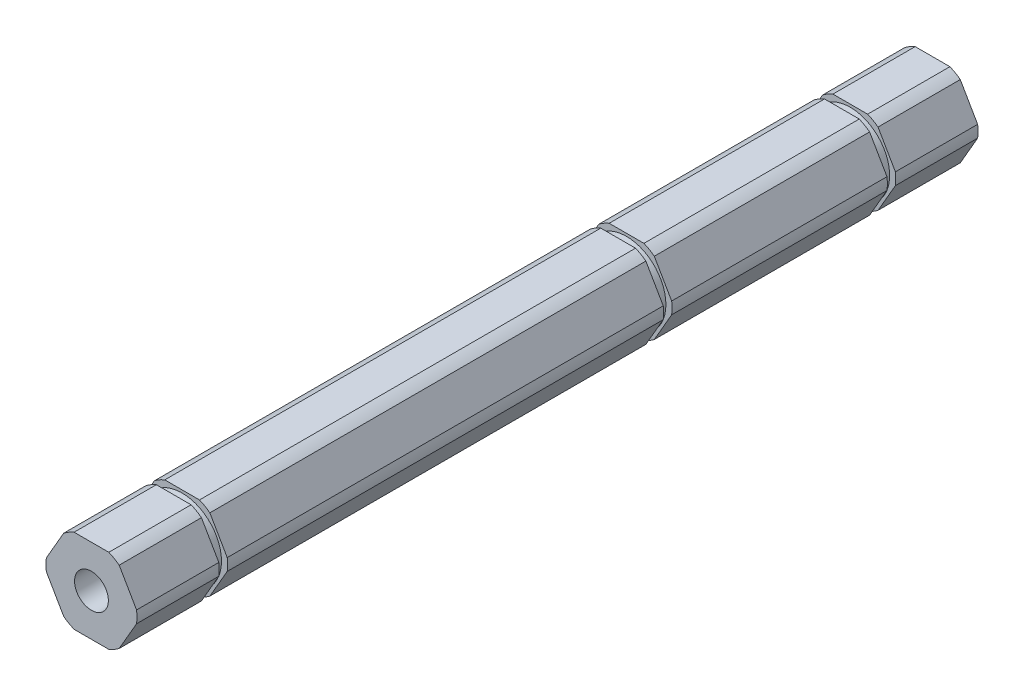
SolidWorks part; units mm, degrees
ref_plane "Front" through (0, 0, 0) normal (0, 0, 1) x (1, 0, 0)
ref_plane "Top" through (0, 0, 0) normal (0, 1, 0) x (1, 0, 0)
ref_plane "Right" through (0, 0, 0) normal (1, 0, 0) x (0, 0, -1)
ref_plane "Plane1" through (0, 0, -17.2974) normal (0, 0, 1) x (1, 0, 0)
sketch "Sketch1" plane through (0, 0, -17.2974) normal (0, 0, 1) x (1, 0, 0)
  line L0 (-4.1874, 5.4472) -> (-6.8111, 0.9028)
  line L1 (-6.8111, -0.9028) -> (-4.1874, -5.4472)
  line L2 (-2.6237, -6.35) -> (2.6237, -6.35)
  line L3 (4.1874, -5.4472) -> (6.8111, -0.9028)
  line L4 (6.8111, 0.9028) -> (4.1874, 5.4472)
  line L5 (2.6237, 6.35) -> (-2.6237, 6.35)
  arc A0 (-2.6237, 6.35) -> (-4.1874, 5.4472) centre (0, 0) ccw
  arc A1 (-6.8111, 0.9028) -> (-6.8111, -0.9028) centre (0, 0) ccw
  arc A2 (-4.1874, -5.4472) -> (-2.6237, -6.35) centre (0, 0) ccw
  arc A3 (2.6237, -6.35) -> (4.1874, -5.4472) centre (0, 0) ccw
  arc A4 (6.8111, -0.9028) -> (6.8111, 0.9028) centre (0, 0) ccw
  arc A5 (4.1874, 5.4472) -> (2.6237, 6.35) centre (0, 0) ccw
extrude "Boss-Extrude1" add sketch "Sketch1" against normal blind 32.512
sketch "Sketch2" plane through (0, 0, -49.8094) normal (0, 0, -1) x (-1, 0, 0)
  circle A0 centre (0, 0) radius 5.9436
extrude "Boss-Extrude2" add sketch "Sketch2" along normal blind 1.27
sketch "Sketch3" plane through (0, 0, -17.2974) normal (0, 0, 1) x (1, 0, 0)
  circle A0 centre (0, 0) radius 5.9436
extrude "Boss-Extrude3" add sketch "Sketch3" along normal blind 1.27
ref_plane "Plane2" through (0, 0, -16.0274) normal (0, 0, -1) x (-1, 0, 0)
sketch "Sketch4" plane through (0, 0, -16.0274) normal (0, 0, -1) x (-1, 0, 0)
  line L0 (2.6237, 6.35) -> (-2.6237, 6.35)
  line L1 (-4.1874, 5.4472) -> (-6.8111, 0.9028)
  line L2 (-6.8111, -0.9028) -> (-4.1874, -5.4472)
  line L3 (-2.6237, -6.35) -> (2.6237, -6.35)
  line L4 (4.1874, -5.4472) -> (6.8111, -0.9028)
  line L5 (6.8111, 0.9028) -> (4.1874, 5.4472)
  arc A0 (4.1874, 5.4472) -> (2.6237, 6.35) centre (0, 0) ccw
  arc A1 (-2.6237, 6.35) -> (-4.1874, 5.4472) centre (0, 0) ccw
  arc A2 (-6.8111, 0.9028) -> (-6.8111, -0.9028) centre (0, 0) ccw
  arc A3 (-4.1874, -5.4472) -> (-2.6237, -6.35) centre (0, 0) ccw
  arc A4 (2.6237, -6.35) -> (4.1874, -5.4472) centre (0, 0) ccw
  arc A5 (6.8111, -0.9028) -> (6.8111, 0.9028) centre (0, 0) ccw
extrude "Boss-Extrude4" add sketch "Sketch4" against normal blind 65.8368
ref_plane "Plane3" through (0, 0, -51.0794) normal (0, 0, 1) x (1, 0, 0)
sketch "Sketch5" plane through (0, 0, -51.0794) normal (0, 0, 1) x (1, 0, 0)
  line L0 (-4.1874, 5.4472) -> (-6.8111, 0.9028)
  line L1 (-6.8111, -0.9028) -> (-4.1874, -5.4472)
  line L2 (-2.6237, -6.35) -> (2.6237, -6.35)
  line L3 (4.1874, -5.4472) -> (6.8111, -0.9028)
  line L4 (6.8111, 0.9028) -> (4.1874, 5.4472)
  line L5 (2.6237, 6.35) -> (-2.6237, 6.35)
  arc A0 (-2.6237, 6.35) -> (-4.1874, 5.4472) centre (0, 0) ccw
  arc A1 (-6.8111, 0.9028) -> (-6.8111, -0.9028) centre (0, 0) ccw
  arc A2 (-4.1874, -5.4472) -> (-2.6237, -6.35) centre (0, 0) ccw
  arc A3 (2.6237, -6.35) -> (4.1874, -5.4472) centre (0, 0) ccw
  arc A4 (6.8111, -0.9028) -> (6.8111, 0.9028) centre (0, 0) ccw
  arc A5 (4.1874, 5.4472) -> (2.6237, 6.35) centre (0, 0) ccw
extrude "Boss-Extrude5" add sketch "Sketch5" against normal blind 12.4206
sketch "Sketch6" plane through (0, 0, 49.8094) normal (0, 0, 1) x (1, 0, 0)
  circle A0 centre (0, 0) radius 5.9436
extrude "Boss-Extrude6" add sketch "Sketch6" along normal blind 1.27
ref_plane "Plane4" through (0, 0, 51.0794) normal (0, 0, -1) x (-1, 0, 0)
sketch "Sketch7" plane through (0, 0, 51.0794) normal (0, 0, -1) x (-1, 0, 0)
  line L0 (6.8111, 0.9028) -> (4.1874, 5.4472)
  line L1 (2.6237, 6.35) -> (-2.6237, 6.35)
  line L2 (-4.1874, 5.4472) -> (-6.8111, 0.9028)
  line L3 (-6.8111, -0.9028) -> (-4.1874, -5.4472)
  line L4 (-2.6237, -6.35) -> (2.6237, -6.35)
  line L5 (4.1874, -5.4472) -> (6.8111, -0.9028)
  arc A0 (4.1874, 5.4472) -> (2.6237, 6.35) centre (0, 0) ccw
  arc A1 (-2.6237, 6.35) -> (-4.1874, 5.4472) centre (0, 0) ccw
  arc A2 (-6.8111, 0.9028) -> (-6.8111, -0.9028) centre (0, 0) ccw
  arc A3 (-4.1874, -5.4472) -> (-2.6237, -6.35) centre (0, 0) ccw
  arc A4 (2.6237, -6.35) -> (4.1874, -5.4472) centre (0, 0) ccw
  arc A5 (6.8111, -0.9028) -> (6.8111, 0.9028) centre (0, 0) ccw
extrude "Boss-Extrude7" add sketch "Sketch7" against normal blind 12.4206
hole_wizard "#7 (0.201) Diameter Hole1" positions "Sketch9" profile "Sketch8" hole size "#7" standard "ANSI Inch"
sketch "Sketch9" plane through (0, 0, -63.5) normal (0, 0, -1) x (-1, 0, 0)
  point P0 (0, 0)
sketch "Sketch8" plane through (0, 0, -63.5) normal (1, 0, 0) x (0, 1, 0)
  line L0 (0, 0) -> (0, 127)
  line L1 (0, 127) -> (2.5527, 127)
  line L2 (2.5527, 127) -> (2.5527, 0)
  line L5 (2.5527, 0) -> (0, 0)
  line L11 (0, -6.35) -> (0, 107.95) construction
  dimension "Thru Hole Dia." = 5.1054
  dimension "Thru Hole Depth" = 127
